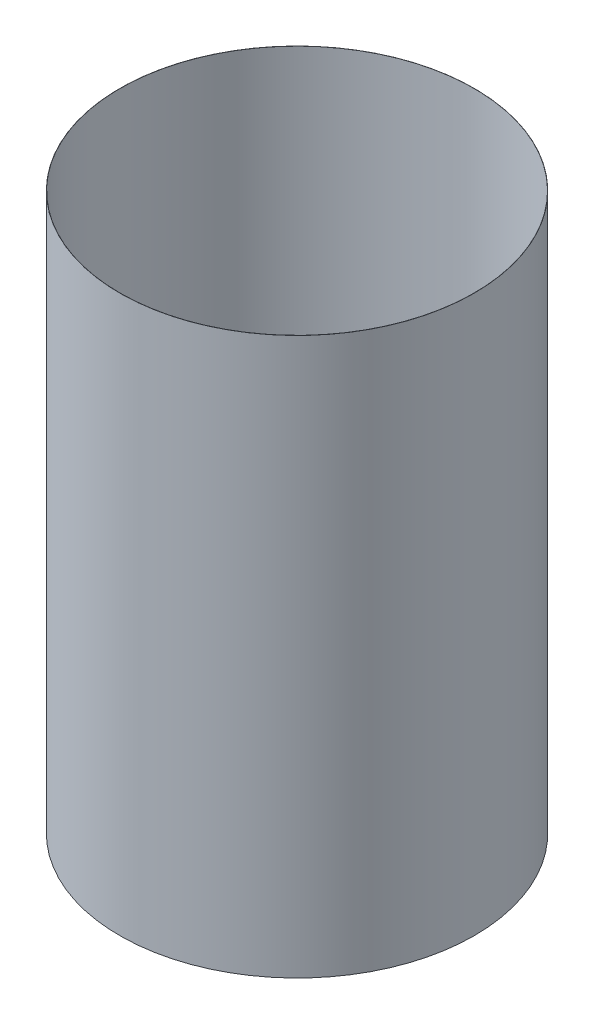
SolidWorks part; units mm, degrees
ref_plane "Plan de face" through (0, 0, 0) normal (0, 0, 1) x (1, 0, 0)
ref_plane "Plan de dessus" through (0, 0, 0) normal (0, 1, 0) x (1, 0, 0)
ref_plane "Plan de droite" through (0, 0, 0) normal (1, 0, 0) x (0, 0, -1)
sketch "Esquisse1" plane through (0, 0, 0) normal (0, 1, 0) x (1, 0, 0)
  circle A0 centre (0, 0) radius 111.4085
  dimension "D1" = 222.8169
extrude "Extru.-Mince1" add sketch "Esquisse1" along normal blind 350 thin
